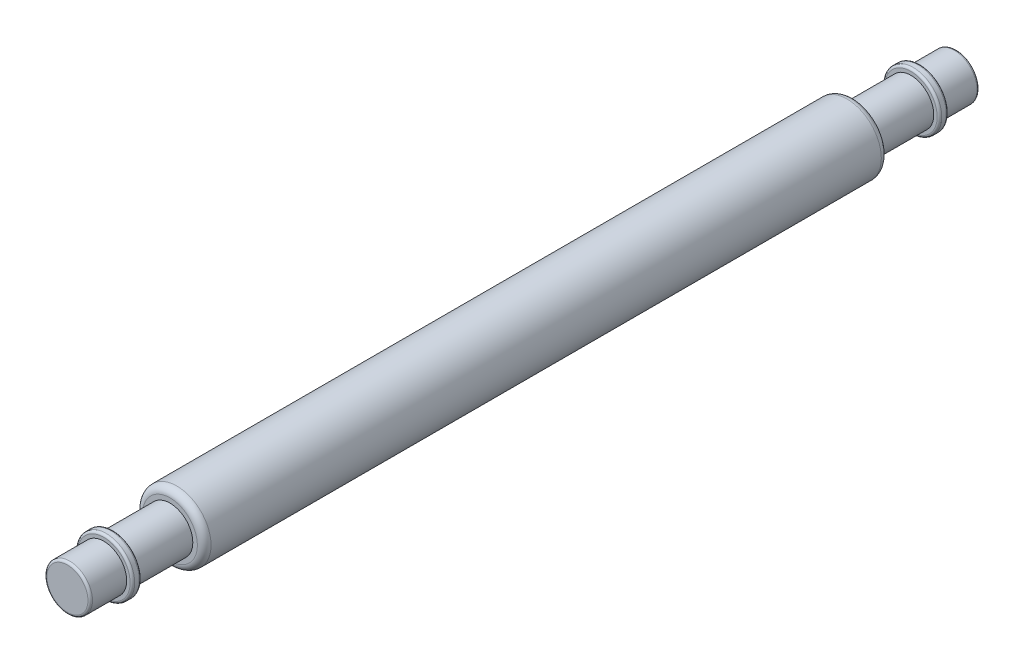
SolidWorks part; units mm, degrees
ref_plane "Front Plane" through (0, 0, 0) normal (0, 0, 1) x (1, 0, 0)
ref_plane "Top Plane" through (0, 0, 0) normal (0, 1, 0) x (1, 0, 0)
ref_plane "Right Plane" through (0, 0, 0) normal (1, 0, 0) x (0, 0, -1)
sketch "Sketch1" plane through (0, 0, 0) normal (0, 0, 1) x (1, 0, 0)
  circle A0 centre (0, 0) radius 0.75
  dimension "D1" = 1.5
extrude "Boss-Extrude1" add sketch "Sketch1" along normal mid plane 15
sketch "Sketch2" plane through (0, 0, 0) normal (0, 0, 1) x (1, 0, 0)
  circle A0 centre (0, 0) radius 0.5
  dimension "D1" = 1
extrude "Boss-Extrude2" add sketch "Sketch2" along normal mid plane 19.5
fillet "Fillet1" radius 0.15 2 edges at (0.75, 0, 7.5) (0.75, 0, -7.5)
fillet "Fillet2" radius 0.05 2 edges at (0.5, 0, 9.75) (0.5, 0, -9.75)
sketch "Sketch3" plane through (0, 0, 9.75) normal (0, 0, 1) x (1, 0, 0)
  circle A0 centre (0, 0) radius 0.625
  dimension "D1" = 1.25
extrude "Boss-Extrude3" add sketch "Sketch3" against normal blind 0.2 from offset 0.8 offset against normal yes
fillet "Fillet3" radius 0.05 2 edges at (0.625, 0, 8.95) (0.625, 0, 8.75)
mirror "Mirror1" about plane through (0, 0, 0) normal (0, 0, 1) of "Fillet3", "Boss-Extrude3"
